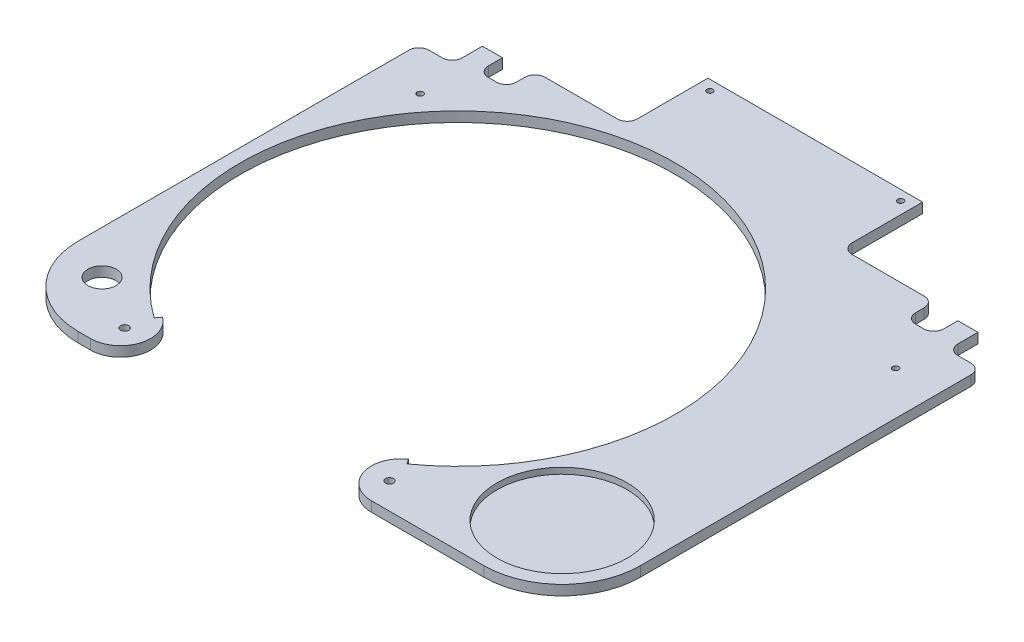
SolidWorks part; units mm, degrees
material "ABS PC"
ref_plane "Plan de face" through (0, 0, 0) normal (0, 0, 1) x (1, 0, 0)
ref_plane "Plan de dessus" through (0, 0, 0) normal (0, 1, 0) x (1, 0, 0)
ref_plane "Plan de droite" through (0, 0, 0) normal (1, 0, 0) x (0, 0, -1)
sketch "Esquisse1" plane through (0, 0, 0) normal (0, 1, 0) x (1, 0, 0)
  line L0 (-101.1, -245.0829) -> (-95, -245.0829) construction
  line L1 (-140.1, 31.2) -> (140.1, 31.2)
  line L2 (-140.1, 31.2) -> (-140.1, -245.0829)
  line L3 (-140.1, -245.0829) -> (140.1, -245.0829)
  line L4 (140.1, 31.2) -> (140.1, -245.0829)
  line L8 (-114.5, 31.2) -> (114.5, 31.2) construction
  line L9 (-140.1, 4) -> (-140.1, -4) construction
  line L10 (140.1, -4) -> (140.1, 4) construction
extrude "Boss.-Extru.1" add sketch "Esquisse1" along normal blind 5
sketch "Esquisse2" plane through (0, 5, 0) normal (0, 1, 0) x (1, 0, 0)
  line L1 (-86.2863, -217.8734) -> (-88.029, -220.3153) construction
  line L2 (-86.2863, -217.8734) -> (-88.029, -220.3153)
  line L3 (45, -245.0829) -> (-95, -245.0829)
  line L5 (36.2863, -217.8734) -> (38.029, -220.3153)
  line L6 (-140.1, -245.0829) -> (140.1, -245.0829) construction
  line L7 (36.2863, -217.8734) -> (38.029, -220.3153) construction
  arc A0 (-95, -245.0829) -> (-86.2863, -217.8734) centre (-95, -230.0829) ccw construction
  arc A2 (-25, -23.5) -> (-88.029, -220.3153) centre (-25, -132) ccw construction
  arc A3 (-25, -23.5) -> (-88.029, -220.3153) centre (-25, -132) ccw
  arc A4 (-95, -245.0829) -> (-86.2863, -217.8734) centre (-95, -230.0829) ccw
  arc A6 (36.2863, -217.8734) -> (45, -245.0829) centre (45, -230.0829) ccw
  arc A7 (38.029, -220.3153) -> (-25, -23.5) centre (-25, -132) ccw
  arc A8 (36.2863, -217.8734) -> (45, -245.0829) centre (45, -230.0829) ccw construction
extrude "Enlèv. mat.-Extru.1" cut sketch "Esquisse2" against normal through all
sketch "Esquisse4" plane through (0, 5, 0) normal (0, 1, 0) x (1, 0, 0)
  line L0 (140.1, -245.0829) -> (101.1, -245.0829)
  line L1 (140.1, -245.0829) -> (140.1, -206.0829)
  line L2 (-101.1, -245.0829) -> (-140.1, -245.0829)
  line L3 (-140.1, -245.0829) -> (-140.1, -206.0829)
  arc A1 (101.1, -245.0829) -> (140.1, -206.0829) centre (101.1, -206.0829) ccw
  arc A3 (-140.1, -206.0829) -> (-101.1, -245.0829) centre (-101.1, -206.0829) ccw
  arc A4 (101.1, -245.0829) -> (140.1, -206.0829) centre (101.1, -206.0829) ccw construction
  arc A5 (-140.1, -206.0829) -> (-101.1, -245.0829) centre (-101.1, -206.0829) ccw construction
extrude "Enlèv. mat.-Extru.3" cut sketch "Esquisse4" against normal through all
sketch "Esquisse5" plane through (0, 5, 0) normal (0, 1, 0) x (1, 0, 0)
  circle A0 centre (-91, -232) radius 2 construction
  circle A1 centre (-91, -232) radius 2
  circle A2 centre (41, -232) radius 2 construction
  circle A3 centre (41, -232) radius 2
extrude "Enlèv. mat.-Extru.4" cut sketch "Esquisse5" against normal through all
sketch "Esquisse6" plane through (0, 5, 0) normal (0, 1, 0) x (1, 0, 0)
  line L0 (99.5, 0) -> (99.5, 26.9) construction
  line L1 (140.1, 31.2) -> (0, 31.2)
  line L2 (140.1, 31.2) -> (140.1, -41.25)
  line L3 (135.1, -36.25) -> (128.5, -36.25)
  line L4 (99.5, -24) -> (99.5, -28.25)
  line L5 (94.5, -19) -> (58.5, -19)
  line L6 (53.5, -14) -> (53.5, 21.2)
  line L7 (53.5, 21.2) -> (-53.5, 21.2)
  line L8 (-82.5, 21.2) -> (82.5, 21.2) construction
  line L9 (55.5, 15) -> (55.5, -15) construction
  line L10 (88, -16) -> (89, -16) construction
  line L11 (-53.5, -14) -> (-53.5, 21.2)
  line L12 (-94.5, -19) -> (-58.5, -19)
  line L13 (-99.5, -24) -> (-99.5, -28.25)
  line L14 (129.94, -36.25) -> (140.1, -36.25) construction
  line L15 (-135.1, -36.25) -> (-128.5, -36.25)
  line L16 (-140.1, 31.2) -> (-140.1, -41.25)
  line L17 (-140.1, 31.2) -> (0, 31.2)
  line L18 (113.5, -28.25) -> (113.5, -21.2)
  line L19 (113.5, -21.2) -> (123.5, -21.2)
  line L20 (123.5, -21.2) -> (123.5, -31.25)
  line L21 (108.5, -33.25) -> (104.5, -33.25)
  line L22 (-123.5, -21.2) -> (-123.5, -31.25)
  line L23 (-113.5, -21.2) -> (-123.5, -21.2)
  line L24 (-113.5, -28.25) -> (-113.5, -21.2)
  line L25 (0, 0) -> (0, 86.4947) construction
  line L26 (-108.5, -33.25) -> (-104.5, -33.25)
  line L27 (140.1, 36.25) -> (140.1, -245.0829) construction
  line L36 (140.1, 31.2) -> (-140.1, 31.2) construction
  arc A0 (140.1, -41.25) -> (135.1, -36.25) centre (135.1, -41.25) ccw
  arc A1 (-99.5, -24) -> (-94.5, -19) centre (-94.5, -24) cw
  arc A2 (58.5, -19) -> (53.5, -14) centre (58.5, -14) cw
  arc A3 (-104.5, -33.25) -> (-99.5, -28.25) centre (-104.5, -28.25) ccw
  arc A4 (104.5, -33.25) -> (99.5, -28.25) centre (104.5, -28.25) cw
  arc A5 (99.5, -24) -> (94.5, -19) centre (94.5, -24) ccw
  arc A6 (-58.5, -19) -> (-53.5, -14) centre (-58.5, -14) ccw
  arc A7 (-140.1, -41.25) -> (-135.1, -36.25) centre (-135.1, -41.25) cw
  arc A8 (113.5, -28.25) -> (108.5, -33.25) centre (108.5, -28.25) cw
  arc A9 (123.5, -31.25) -> (128.5, -36.25) centre (128.5, -31.25) ccw
  arc A10 (-123.5, -31.25) -> (-128.5, -36.25) centre (-128.5, -31.25) cw
  arc A11 (-113.5, -28.25) -> (-108.5, -33.25) centre (-108.5, -28.25) ccw
  point P41 (99.5, -36.25)
  point P43 (99.5, -19)
  point P49 (0, 21.2)
  point P58 (113.5, -33.25)
  dimension "D1" = 5
  dimension "D4" = 3
  dimension "D2" = 2
  dimension "D3" = 3
extrude "Enlèv. mat.-Extru.5" cut sketch "Esquisse6" against normal through all
sketch "Esquisse7" plane through (0, 5, 0) normal (0, 1, 0) x (1, 0, 0)
  circle A1 centre (-118.5, -215.8) radius 7.0711
extrude "Enlèv. mat.-Extru.6" cut sketch "Esquisse7" against normal through all
sketch "Esquisse8" plane through (0, 0, 0) normal (0, -1, 0) x (1, 0, 0)
  line L1 (-114.5, -21.2) -> (114.5, -21.2) construction
  line L2 (0, 0) -> (0, -63.4963) construction
  circle A1 centre (47.5, -16.2) radius 1.5
  circle A2 centre (-47.5, -16.2) radius 1.5
  dimension "D4" = 3
  dimension "D2" = 5
  dimension "D3" = 95
extrude "Enlèv. mat.-Extru.8" cut sketch "Esquisse8" against normal through all
sketch "Esquisse9" plane through (0, 5, 0) normal (0, 1, 0) x (1, 0, 0)
  circle A0 centre (101.1, -206.0829) radius 32.5
  circle A1 centre (101.1, -206.0829) radius 32 construction
  dimension "D1" = 65
extrude "Enlèv. mat.-Extru.10" cut sketch "Esquisse9" against normal blind 3
sketch "Esquisse10" plane through (0, 5, 0) normal (0, 1, 0) x (1, 0, 0)
  line L0 (118.5, -57.265) -> (123.5, -57.265) construction
  line L1 (123.5, -55.765) -> (123.5, -58.765) construction
  line L2 (-123.5, -57.265) -> (-118.5, -57.265) construction
  line L3 (-123.5, -58.765) -> (-123.5, -55.765) construction
  circle A0 centre (118.5, -57.265) radius 1.5
  circle A1 centre (-118.5, -57.265) radius 1.5
  dimension "D2" = 3
  dimension "D1" = 5
extrude "Enlèv. mat.-Extru.11" cut sketch "Esquisse10" against normal through all
sketch "Esquisse11" plane through (0, 5, 0) normal (0, 1, 0) x (1, 0, 0)
  circle A0 centre (118.5, -132) radius 1.5
  circle A1 centre (118.5, -132) radius 1.5 construction
extrude "Enlèv. mat.-Extru.12" [suppressed] cut sketch "Esquisse11" against normal through all
